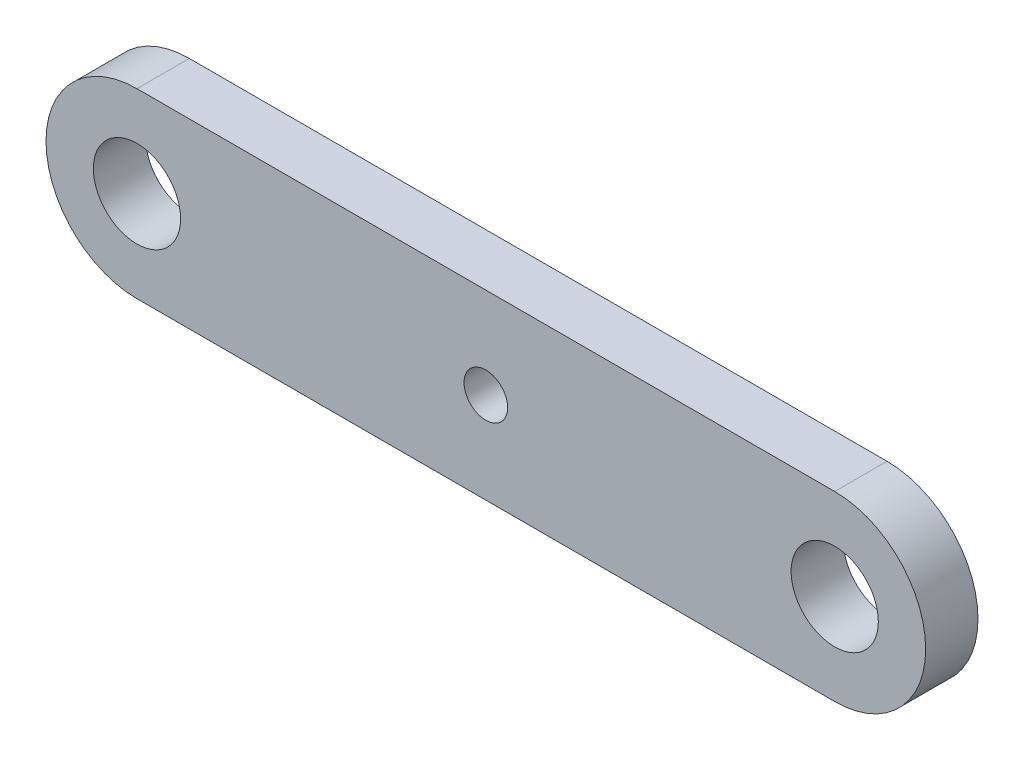
SolidWorks part; units mm, degrees
ref_plane "Alzado" through (0, 0, 0) normal (0, 0, 1) x (1, 0, 0)
ref_plane "Planta" through (0, 0, 0) normal (0, 1, 0) x (1, 0, 0)
ref_plane "Vista lateral" through (0, 0, 0) normal (1, 0, 0) x (0, 0, -1)
sketch "Croquis1" plane through (0, 0, 0) normal (0, 0, 1) x (1, 0, 0)
  line L0 (-42.037, 0) -> (37.963, 0) construction
  line L1 (-42.037, 10.4294) -> (37.963, 10.4294)
  line L2 (-42.037, -10.4294) -> (37.963, -10.4294)
  arc A0 (-42.037, 10.4294) -> (-42.037, -10.4294) centre (-42.037, 0) ccw
  arc A1 (37.963, -10.4294) -> (37.963, 10.4294) centre (37.963, 0) ccw
  circle A2 centre (-42.037, 0) radius 5
  circle A3 centre (37.963, 0) radius 5
  circle A4 centre (-2.037, 0) radius 2.5
  point P3 (-2.037, 0)
  dimension "D2" = 10
  dimension "D3" = 5
  dimension "D1" = 80
extrude "Saliente-Extruir1" add sketch "Croquis1" along normal blind 6
